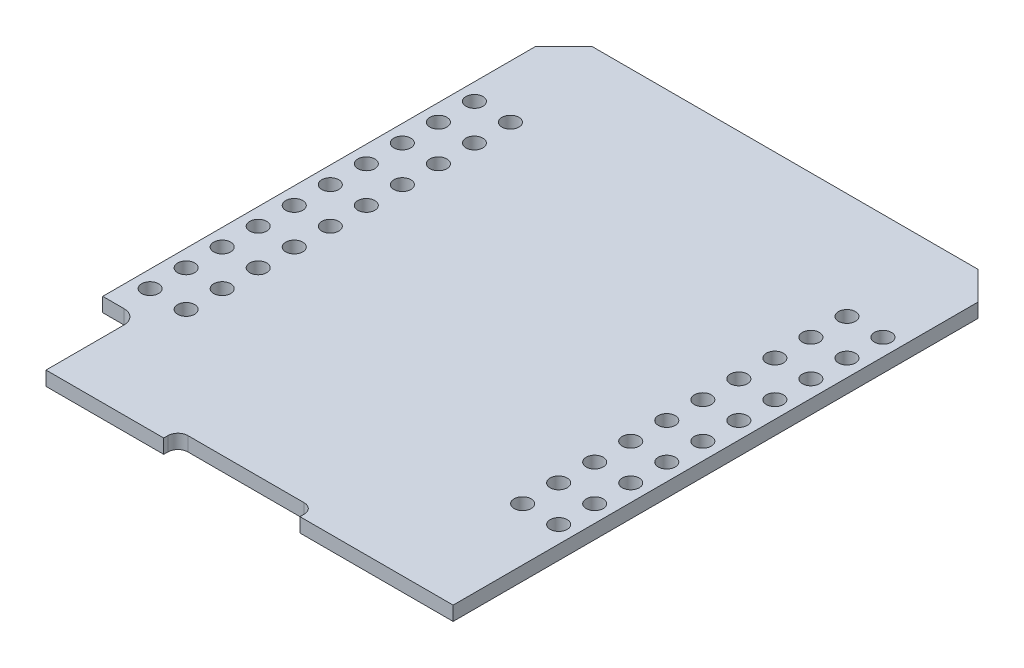
SolidWorks part; units mm, degrees
ref_plane "Plan de face" through (0, 0, 0) normal (0, 0, 1) x (1, 0, 0)
ref_plane "Plan de dessus" through (0, 0, 0) normal (0, 1, 0) x (1, 0, 0)
ref_plane "Plan de droite" through (0, 0, 0) normal (1, 0, 0) x (0, 0, -1)
sketch "Esquisse1" plane through (0, 0, 0) normal (0, 1, 0) x (1, 0, 0)
  line L0 (-13.1, 0) -> (-13.1, 5.5)
  line L1 (-13.6, 39) -> (13.6, 39)
  line L2 (-15.6, 37) -> (-15.6, 6.5)
  line L3 (-13.1, 0) -> (-4.8, 0)
  line L4 (15.6, 37) -> (15.6, 0)
  line L5 (-14.1, 6.5) -> (-15.6, 6.5)
  line L6 (-15.6, 37) -> (-13.6, 39)
  line L7 (15.6, 37) -> (13.6, 39)
  line L8 (-4.8, 0) -> (-4.8, 0.3)
  line L9 (-4.1, 1) -> (4.1, 1)
  line L10 (4.8, 0.3) -> (4.8, 0)
  line L11 (4.8, 0) -> (15.6, 0)
  arc A0 (-13.1, 5.5) -> (-14.1, 6.5) centre (-14.1, 5.5) ccw
  arc A1 (4.8, 0.3) -> (4.1, 1) centre (4.1, 0.3) ccw
  arc A2 (-4.8, 0.3) -> (-4.1, 1) centre (-4.1, 0.3) cw
  point P0 (0, 39)
  point P6 (0, 1)
  point P11 (-13.1, 6.5)
  point P20 (4.8, 1)
  point P23 (-4.8, 1)
  dimension "D5" = 1
  dimension "D12" = 0.7
  dimension "D13" = 0.7
  dimension "D1" = 39
  dimension "D2" = 31.2
  dimension "D3" = 6.5
  dimension "D4" = 2.5
  dimension "D6" = 45
  dimension "D7" = 45
  dimension "D8" = 2
  dimension "D9" = 2
  dimension "D10" = 9.6
  dimension "D11" = 1
extrude "Boss.-Extru.1" add sketch "Esquisse1" along normal blind 1
sketch "Esquisse2" plane through (0, 1, 0) normal (0, 1, 0) x (1, 0, 0)
  line L0 (0, 0) -> (0, 39) construction
  line L1 (13.6, 39) -> (-13.6, 39) construction
  line L2 (15.6, 0) -> (15.6, 37) construction
  circle A0 centre (14.4, 31.5) radius 0.6
  circle A1 centre (11.86, 31.5) radius 0.6
  circle A2 centre (11.86, 28.96) radius 0.6
  circle A3 centre (11.86, 26.42) radius 0.6
  circle A4 centre (11.86, 23.88) radius 0.6
  circle A5 centre (11.86, 21.34) radius 0.6
  circle A6 centre (11.86, 18.8) radius 0.6
  circle A7 centre (11.86, 16.26) radius 0.6
  circle A8 centre (11.86, 13.72) radius 0.6
  circle A9 centre (11.86, 11.18) radius 0.6
  circle A10 centre (11.86, 8.64) radius 0.6
  circle A11 centre (14.4, 28.96) radius 0.6
  circle A12 centre (14.4, 26.42) radius 0.6
  circle A13 centre (14.4, 23.88) radius 0.6
  circle A14 centre (14.4, 21.34) radius 0.6
  circle A15 centre (14.4, 18.8) radius 0.6
  circle A16 centre (14.4, 16.26) radius 0.6
  circle A17 centre (14.4, 13.72) radius 0.6
  circle A18 centre (14.4, 11.18) radius 0.6
  circle A19 centre (14.4, 8.64) radius 0.6
  circle A20 centre (-14.4, 8.64) radius 0.6
  circle A21 centre (-14.4, 11.18) radius 0.6
  circle A22 centre (-14.4, 13.72) radius 0.6
  circle A23 centre (-14.4, 16.26) radius 0.6
  circle A24 centre (-14.4, 18.8) radius 0.6
  circle A25 centre (-14.4, 21.34) radius 0.6
  circle A26 centre (-14.4, 23.88) radius 0.6
  circle A27 centre (-14.4, 26.42) radius 0.6
  circle A28 centre (-14.4, 28.96) radius 0.6
  circle A29 centre (-11.86, 8.64) radius 0.6
  circle A30 centre (-11.86, 11.18) radius 0.6
  circle A31 centre (-11.86, 13.72) radius 0.6
  circle A32 centre (-11.86, 16.26) radius 0.6
  circle A33 centre (-11.86, 18.8) radius 0.6
  circle A34 centre (-11.86, 21.34) radius 0.6
  circle A35 centre (-11.86, 23.88) radius 0.6
  circle A36 centre (-11.86, 26.42) radius 0.6
  circle A37 centre (-11.86, 28.96) radius 0.6
  circle A38 centre (-11.86, 31.5) radius 0.6
  circle A39 centre (-14.4, 31.5) radius 0.6
  dimension "D1" = 1.2
  dimension "D3" = 7.5
  dimension "D2" = 1.2
  dimension "D4" = 2
  dimension "D5" = 10
extrude "Enlèv. mat.-Extru.1" cut sketch "Esquisse2" against normal blind 1
